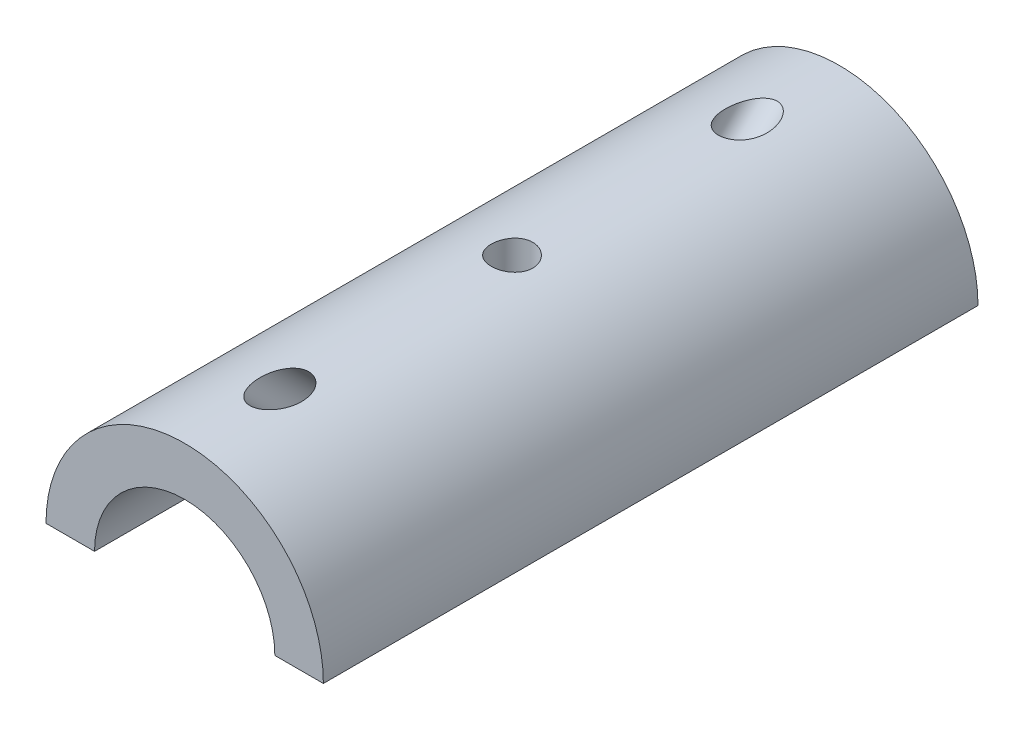
SolidWorks part; units mm, degrees
material "Aluminum Bronze"
ref_plane "Front Plane" through (0, 0, 0) normal (0, 0, 1) x (1, 0, 0)
ref_plane "Top Plane" through (0, 0, 0) normal (0, 1, 0) x (1, 0, 0)
ref_plane "Right Plane" through (0, 0, 0) normal (1, 0, 0) x (0, 0, -1)
sketch "Sketch1" plane through (0, 0, 0) normal (0, 0, 1) x (1, 0, 0)
  line L0 (10, 0) -> (-10, 0)
  circle A0 centre (0, 0) radius 6.5
  circle A1 centre (0, 0) radius 10
extrude "Boss-Extrude1" add sketch "Sketch1" along normal blind 47.2 contours L0 A1 A0
sketch "Sketch3" plane through (0, 0, 0) normal (0, 1, 0) x (1, 0, 0)
  line L0 (-10, 0) -> (0, 0)
  line L1 (0, 0) -> (0, -23.6)
  circle A0 centre (0, -23.6) radius 1.5
extrude "Cut-Extrude1" cut sketch "Sketch3" against normal through all both and the other way through all
sketch "Sketch4" plane through (0, 0, 0) normal (1, 0, 0) x (0, 0, -1)
  line L0 (0, 10) -> (-5.8835, 10)
  line L1 (0, 10) -> (-22.1001, 10) construction
  line L2 (0, 0) -> (0, 10) construction
  dimension "D1" = 5.8835
sketch "Sketch5" plane through (0, 0, 0) normal (1, 0, 0) x (0, 0, -1)
  line L0 (0, 10) -> (-6.6, 10)
  line L1 (0, 10) -> (-22.1001, 10) construction
  line L2 (-6.6, 10) -> (0.4711, 2.9289)
  line L3 (0.4711, 2.9289) -> (-13.6711, 17.0711) construction
  circle A0 centre (-6.6, 10) radius 10
  dimension "D1" = 6.6
ref_plane "Plane1" through (0, 1.7, -1.7) normal (0, 0.7071, -0.7071) x (0, 0.7071, 0.7071)
sketch "Sketch7" plane through (0, 1.7, -1.7) normal (0, 0.7071, -0.7071) x (0, 0.7071, 0.7071)
  circle A0 centre (11.738, 0) radius 1.5
extrude "Cut-Extrude3" cut sketch "Sketch7" against normal through all both and the other way through all
sketch "Sketch9" plane through (0, 0, 0) normal (1, 0, 0) x (0, 0, -1)
  line L0 (-46.9784, 10) -> (-40.3784, 10)
  line L1 (-40.3784, 10) -> (-33.3073, 17.0711)
  line L2 (-33.3073, 17.0711) -> (-47.4494, 2.9289) construction
  circle A0 centre (-40.3784, 10) radius 10
  dimension "D1" = 6.6
ref_plane "Plane2" through (0, 25.1892, 25.1892) normal (0, 0.7071, 0.7071) x (0, -0.7071, 0.7071)
sketch "Sketch10" plane through (0, 25.1892, 25.1892) normal (0, 0.7071, 0.7071) x (0, -0.7071, 0.7071)
  circle A0 centre (21.4808, 0) radius 1.5
extrude "Cut-Extrude4" cut sketch "Sketch10" against normal through all both and the other way through all
